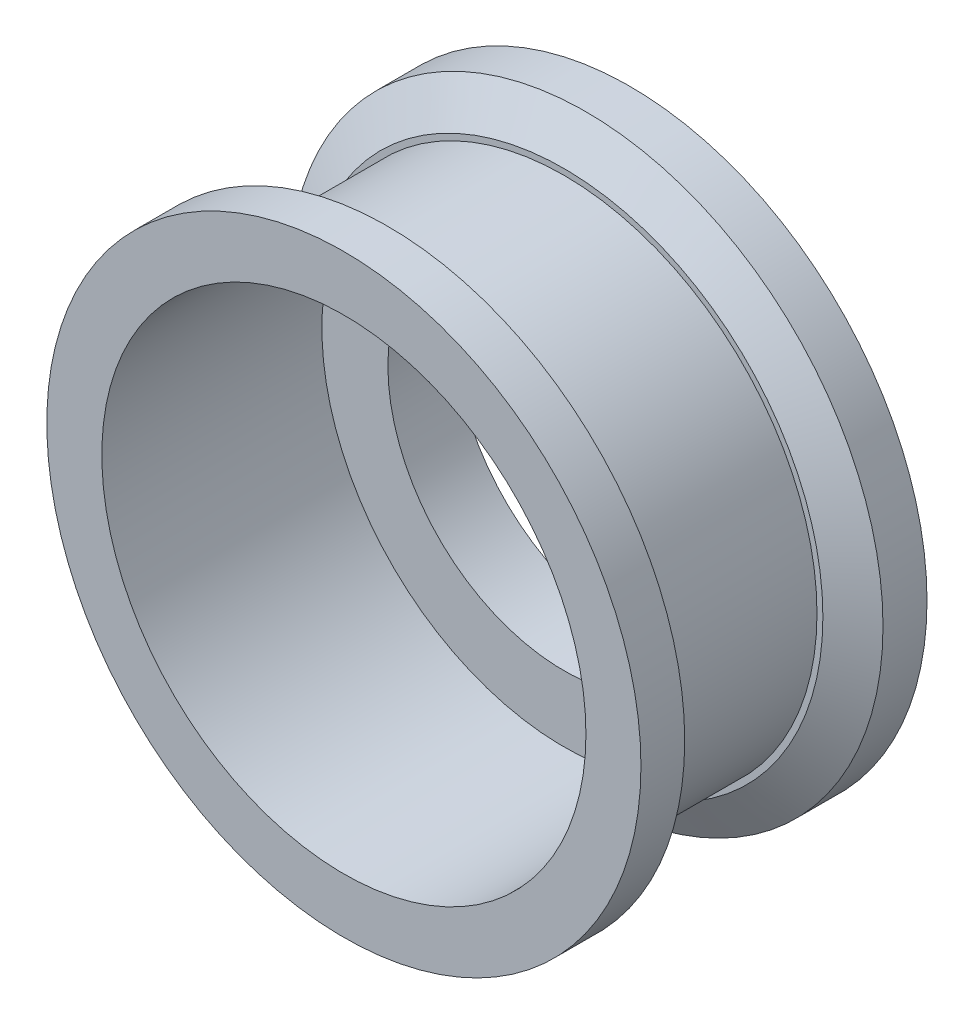
SolidWorks part; units mm, degrees
ref_plane "Front Plane" through (0, 0, 0) normal (0, 0, 1) x (1, 0, 0)
ref_plane "Top Plane" through (0, 0, 0) normal (0, 1, 0) x (1, 0, 0)
ref_plane "Right Plane" through (0, 0, 0) normal (1, 0, 0) x (0, 0, -1)
sketch "Sketch1" plane through (0, 0, 0) normal (0, 0, 1) x (1, 0, 0)
  circle A0 centre (0, 0) radius 13.5
  circle A1 centre (0, 0) radius 8
  dimension "D1" = 27
  dimension "D2" = 16
extrude "Boss-Extrude1" add sketch "Sketch1" along normal blind 13
sketch "Sketch2" plane through (0, 0, 13) normal (0, 0, 1) x (1, 0, 0)
  circle A0 centre (0, 0) radius 11
  dimension "D1" = 22
extrude "Cut-Extrude1" cut sketch "Sketch2" against normal blind 10
sketch "Sketch3" plane through (0, 0, 13) normal (0, 0, 1) x (1, 0, 0)
  circle A0 centre (0, 0) radius 11.5
  dimension "D1" = 23
extrude "Cut-Extrude2" cut sketch "Sketch3" against normal blind 7 from offset 3 flip side to cut offset against normal yes
chamfer "Chamfer1" distance 1.75 angle 30 1 edges at (13.5, 0, 10)
chamfer "Chamfer2" distance 1 angle 60 1 edges at (13.5, 0, 3)
